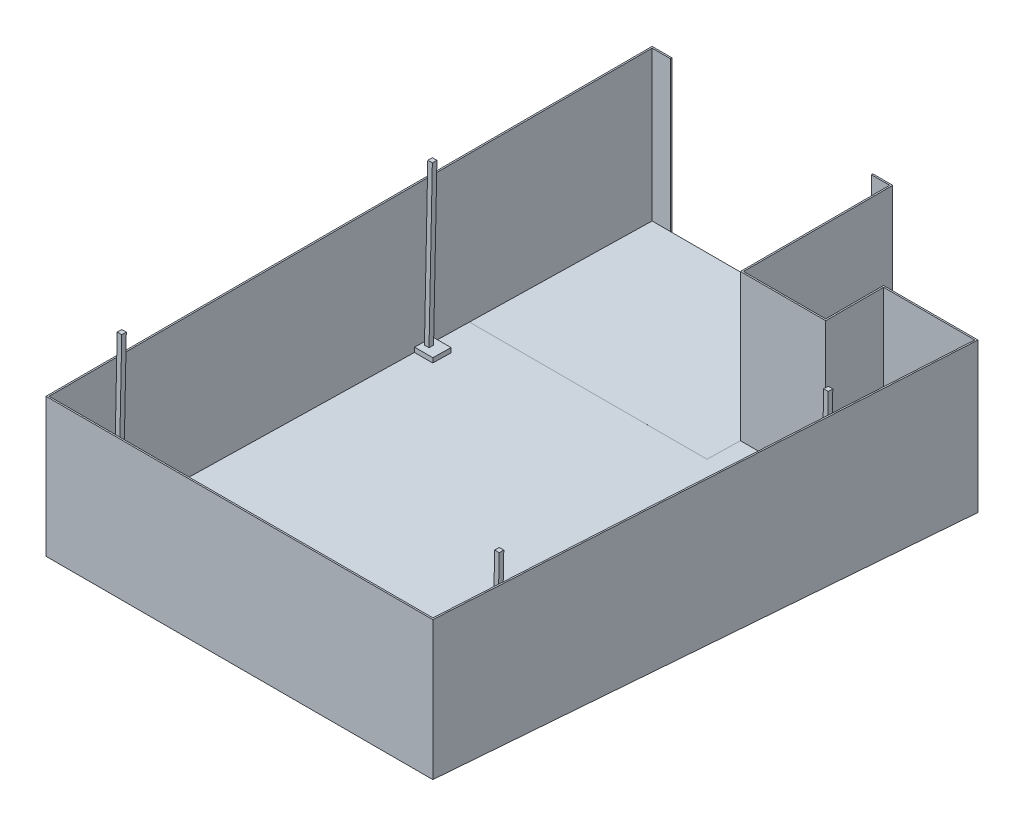
SolidWorks part; units mm, degrees
ref_plane "Front Plane" through (0, 0, 0) normal (0, 0, 1) x (1, 0, 0)
ref_plane "Top Plane" through (0, 0, 0) normal (0, 1, 0) x (1, 0, 0)
ref_plane "Right Plane" through (0, 0, 0) normal (1, 0, 0) x (0, 0, -1)
sketch "Sketch2" plane through (0, 0, 0) normal (0, 1, 0) x (1, 0, 0)
  line L0 (0, 5054.6) -> (0, -5054.6)
  line L1 (0, -5054.6) -> (6451.6, -5054.6)
  line L2 (6451.6, -5054.6) -> (6959.6, 3530.6)
  line L3 (4013.2, 5054.6) -> (0, 5054.6)
  line L4 (4013.2, 5054.6) -> (4013.2, 2565.4)
  line L5 (4013.2, 2565.4) -> (5384.8, 2565.4)
  line L6 (5384.8, 2565.4) -> (5384.8, 3530.6)
  line L7 (5384.8, 3530.6) -> (6959.6, 3530.6)
  point P16 (0, 0)
  dimension "D1" = 10109.2
  dimension "D2" = 4013.2
  dimension "D3" = 6451.6
  dimension "D4" = 2489.2
  dimension "D5" = 6959.6
  dimension "D6" = 965.2
  dimension "D7" = 1574.8
extrude "Boss-Extrude2" add sketch "Sketch2" along normal blind 2311.4 and the other way blind 254
sketch "Sketch4" plane through (0, 0, 0) normal (-1, 0, 0) x (0, 0, 1)
  line L0 (5054.6, 0) -> (-5054.6, -211.7576)
  line L1 (5054.6, -254) -> (5054.6, 2311.4) construction
  line L4 (-5054.6, -254) -> (-5054.6, 2311.4) construction
  line L5 (-5054.6, -211.7576) -> (-5054.6, -254)
  line L6 (-5054.6, -254) -> (5054.6, -254)
  line L7 (5054.6, -254) -> (5054.6, 0)
  dimension "D1" = 1.2
extrude "Cut-Extrude1" cut sketch "Sketch4" against normal through all
shell "Shell3" thickness 25.4
sketch "Sketch5" plane through (0, -80.4379, 1.6849) normal (0, 0.9998, -0.0209) x (1, 0, 0)
  line L1 (25.4, -4114.2179) -> (330.2, -4114.2179)
  line L2 (330.2, -4114.2179) -> (330.2, -3809.4179)
  line L3 (330.2, -3809.4179) -> (25.4, -3809.4179)
  line L4 (6427.6585, -5028.6179) -> (25.4, -5028.6179) construction
  line L5 (25.4, -5028.6179) -> (25.4, 5031.9885) construction
  line L10 (25.4, 1067.3821) -> (330.2, 1067.3821)
  line L15 (330.2, 1067.3821) -> (330.2, 1372.1821)
  line L16 (330.2, 1372.1821) -> (25.4, 1372.1821)
  line L17 (6501.521, 1067.3821) -> (6788.2895, 1067.3821)
  line L18 (25.4, 1372.1821) -> (25.4, 1067.3821)
  line L19 (25.4, -4114.2179) -> (25.4, -3809.4179)
  line L20 (6194.4518, -4114.2179) -> (6481.7532, -4114.2179)
  line L22 (6499.7847, -3809.4179) -> (6194.4518, -3809.4179)
  line L23 (6194.4518, -4114.2179) -> (6194.4518, -3809.4179)
  line L25 (6932.6526, 3507.6542) -> (6427.6585, -5028.6179) construction
  line L26 (6806.321, 1372.1821) -> (6501.521, 1372.1821)
  line L27 (6501.521, 1067.3821) -> (6501.521, 1372.1821)
  line L28 (6806.321, 1372.1821) -> (6788.2895, 1067.3821)
  line L29 (6499.7847, -3809.4179) -> (6481.7532, -4114.2179)
  dimension "D1" = 304.8
  dimension "D2" = 914.4
  dimension "D3" = 304.8
  dimension "D4" = 304.8
  dimension "D5" = 304.8
  dimension "D7" = 5181.6
  dimension "D8" = 304.8
extrude "Boss-Extrude4" add sketch "Sketch5" along normal blind 76.2
sketch "Sketch6" plane through (0, -4.2546, 0.0891) normal (0, 0.9998, -0.0209) x (1, 0, 0)
  line L0 (76.2, 1257.8821) -> (76.2, 1181.6821)
  line L1 (76.2, 1181.6821) -> (152.4, 1181.6821)
  line L2 (152.4, 1181.6821) -> (152.4, 1257.8821)
  line L3 (152.4, 1257.8821) -> (76.2, 1257.8821)
  line L4 (76.2, -3923.7179) -> (76.2, -3999.9179)
  line L5 (76.2, -3999.9179) -> (152.4, -3999.9179)
  line L6 (152.4, -3999.9179) -> (152.4, -3923.7179)
  line L7 (152.4, -3923.7179) -> (76.2, -3923.7179)
  line L8 (6372.2518, -3923.7179) -> (6372.2518, -3999.9179)
  line L9 (6372.2518, -3999.9179) -> (6448.4518, -3999.9179)
  line L10 (6448.4518, -3999.9179) -> (6448.4518, -3923.7179)
  line L11 (6448.4518, -3923.7179) -> (6372.2518, -3923.7179)
  line L12 (6679.321, 1257.8821) -> (6679.321, 1181.6821)
  line L13 (6679.321, 1181.6821) -> (6755.521, 1181.6821)
  line L14 (6755.521, 1181.6821) -> (6755.521, 1257.8821)
  line L15 (6755.521, 1257.8821) -> (6679.321, 1257.8821)
  line L16 (330.2, 1067.3821) -> (330.2, 1372.1821) construction
  line L17 (330.2, -4114.2179) -> (330.2, -3809.4179) construction
  line L18 (25.4, 1372.1821) -> (25.4, 1067.3821) construction
  line L21 (6194.4518, -3809.4179) -> (6194.4518, -4114.2179) construction
  line L22 (6501.521, 1372.1821) -> (6501.521, 1067.3821) construction
  point P18 (330.2, 1219.7821)
  point P19 (152.4, 1219.7821)
  point P20 (6679.321, 1219.7821)
  point P23 (330.2, -3961.8179)
  point P24 (152.4, -3961.8179)
  point P25 (6372.2518, -3961.8179)
  dimension "D1" = 76.2
  dimension "D2" = 50.8
  dimension "D3" = 177.8
  dimension "D4" = 177.8
sketch3d "3DSketch1"
  point P0 (5144.6677, 2311.4, 5044.2382)
ref_plane "Plane3" through (0, 2313.94, 0) normal (0, 1, 0) x (1, 0, 0)
extrude "Boss-Extrude6" add sketch "Sketch6" along normal blind 2643.378
sketch "Sketch7" plane through (0, -80.4379, 1.6849) normal (0, 0.9998, -0.0209) x (1, 0, 0)
  line L0 (0, 1983.9885) -> (3987.8, 1983.9885)
  line L1 (0, 5058.8108) -> (0, -5048.1721) construction
  line L2 (3987.8, 1983.9885) -> (3987.8, 5031.9885)
  line L3 (3987.8, 5031.9885) -> (25.4, 5031.9885) construction
  line L4 (0, 1983.9885) -> (25.4, 5031.9885)
  line L5 (25.4, 5031.9885) -> (3987.8, 5031.9885)
  dimension "D1" = 3048
extrude "Boss-Extrude7" add sketch "Sketch7" along normal blind 0.0254
sketch "Sketch8" plane through (0, 0, -5054.6) normal (0, 0, -1) x (-1, 0, 0)
  line L0 (-3683, 2311.4) -> (-330.2, 2311.4)
  line L1 (-4013.2, 2311.4) -> (0, 2311.4) construction
  line L2 (-330.2, 2311.4) -> (-330.2, -211.7576)
  line L3 (-4013.2, -211.7576) -> (0, -211.7576) construction
  line L4 (-330.2, -211.7576) -> (-3683, -211.7576)
  line L5 (-3683, -211.7576) -> (-3683, 2311.4)
  line L6 (0, -211.7576) -> (0, 2311.4) construction
  line L7 (-4013.2, -211.7576) -> (-4013.2, 2311.4) construction
  dimension "D1" = 330.2
  dimension "D2" = 330.2
extrude "Cut-Extrude2" cut sketch "Sketch8" against normal up to surface (25.4 mm away) up to face at (2006.6, 1062.8027, -5029.2)
